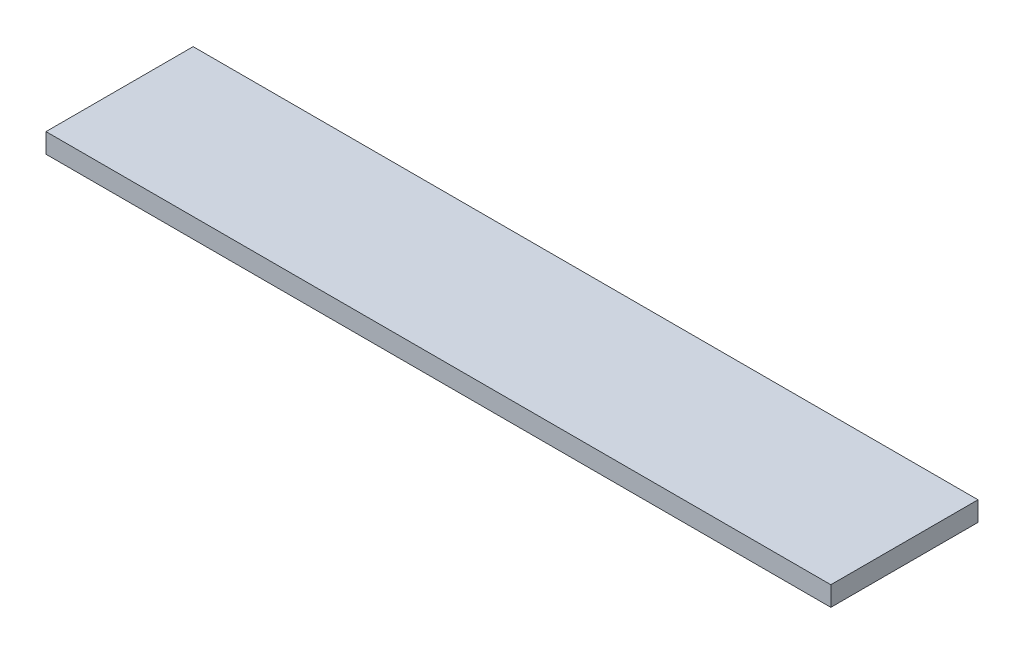
SolidWorks part; units mm, degrees
ref_plane "Спереди" through (0, 0, 0) normal (0, 0, 1) x (1, 0, 0)
ref_plane "Сверху" through (0, 0, 0) normal (0, 1, 0) x (1, 0, 0)
ref_plane "Справа" through (0, 0, 0) normal (1, 0, 0) x (0, 0, -1)
sketch "Эскиз1" plane through (0, 0, 0) normal (0, 1, 0) x (1, 0, 0)
  line L1 (-400, 75) -> (400, 75)
  line L2 (-400, 75) -> (-400, -75)
  line L3 (-400, -75) -> (400, -75)
  line L4 (400, 75) -> (400, -75)
  line L5 (-400, 75) -> (400, -75) construction
  line L6 (-400, -75) -> (400, 75) construction
  point P0 (0, 0)
extrude "Бобышка-Вытянуть1" add sketch "Эскиз1" along normal blind 20
